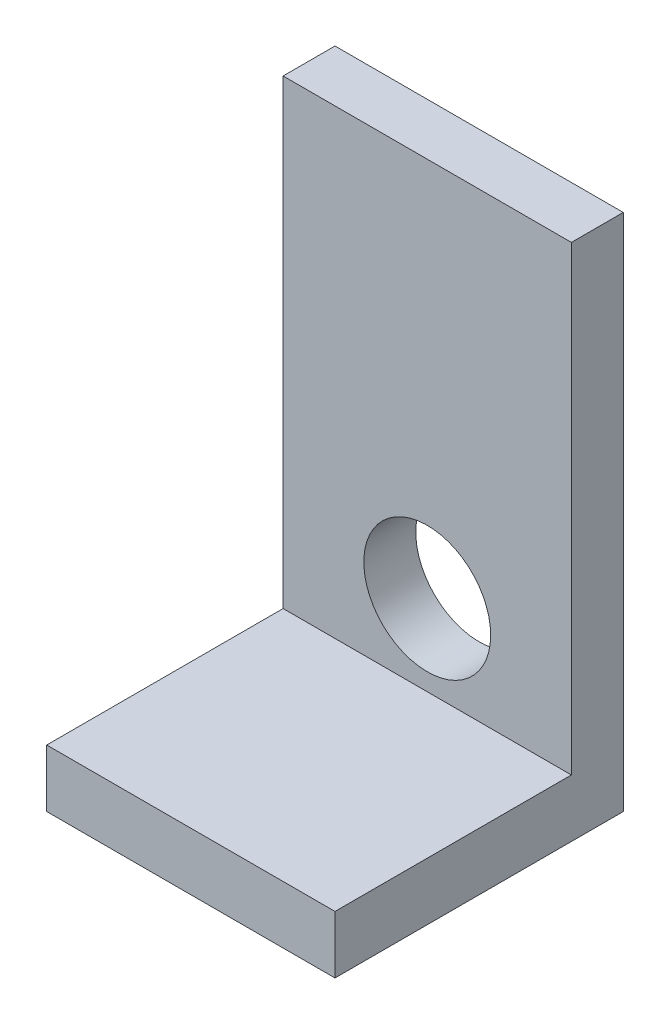
SolidWorks part; units mm, degrees
ref_plane "Front Plane" through (0, 0, 0) normal (0, 0, 1) x (1, 0, 0)
ref_plane "Top Plane" through (0, 0, 0) normal (0, 1, 0) x (1, 0, 0)
ref_plane "Right Plane" through (0, 0, 0) normal (1, 0, 0) x (0, 0, -1)
sketch "Sketch1" plane through (0, 0, 0) normal (0, 1, 0) x (1, 0, 0)
  line L1 (-3.175, 3.175) -> (3.175, 3.175)
  line L2 (-3.175, 3.175) -> (-3.175, -3.175)
  line L3 (-3.175, -3.175) -> (3.175, -3.175)
  line L4 (3.175, 3.175) -> (3.175, -3.175)
  line L5 (-3.175, 3.175) -> (3.175, -3.175) construction
  line L6 (-3.175, -3.175) -> (3.175, 3.175) construction
  point P0 (0, 0)
extrude "Boss-Extrude1" add sketch "Sketch1" along normal blind 1.27
sketch "Sketch2" plane through (0, 1.27, 0) normal (0, 1, 0) x (1, 0, 0)
  line L0 (3.175, -3.175) -> (3.175, 3.175) construction
  line L1 (-3.175, 3.175) -> (3.175, 3.175)
  line L2 (-3.175, 3.175) -> (-3.175, 2.032)
  line L3 (-3.175, 2.032) -> (3.175, 2.032)
  line L4 (3.175, 3.175) -> (3.175, 2.032)
extrude "Boss-Extrude2" add sketch "Sketch2" along normal blind 10.16
sketch "Sketch4" plane through (0, 0, -2.032) normal (0, 0, 1) x (1, 0, 0)
  circle A0 centre (0, 3.048) radius 1.397
extrude "Cut-Extrude1" cut sketch "Sketch4" against normal up to next
